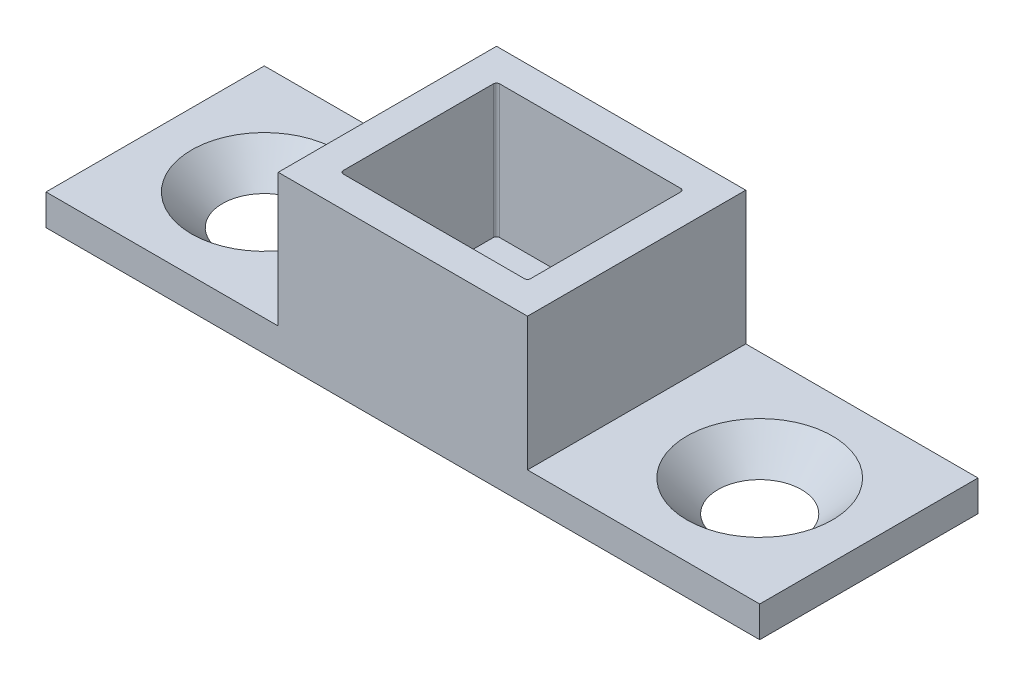
SolidWorks part; units mm, degrees
ref_plane "Front Plane" through (0, 0, 0) normal (0, 0, 1) x (1, 0, 0)
ref_plane "Top Plane" through (0, 0, 0) normal (0, 1, 0) x (1, 0, 0)
ref_plane "Right Plane" through (0, 0, 0) normal (1, 0, 0) x (0, 0, -1)
sketch "Sketch1" plane through (0, 0, 0) normal (0, 1, 0) x (1, 0, 0)
  line L0 (0, 5.05) -> (0, 7.05) construction
  line L1 (-8.05, 7.05) -> (8.05, 7.05)
  line L2 (-8.05, 7.05) -> (-8.05, -7.05)
  line L3 (-8.05, -7.05) -> (8.05, -7.05)
  line L4 (8.05, 7.05) -> (8.05, -7.05)
  line L5 (0, -5.05) -> (0, 0) construction
  line L6 (-8.05, 0) -> (-6.05, 0) construction
  line L11 (0, -5.05) -> (0, 0) construction
  line L12 (0, 0) -> (6.05, 0) construction
  line L13 (0, 0) -> (6.05, 0) construction
  point P233 (0, 0)
  point P296 (0, 0)
  dimension "D1" = 16.1
  dimension "D2" = 14.1
extrude "Boss-Extrude1" add sketch "Sketch1" along normal blind 10.6
sketch "Sketch3" plane through (0, 10.6, 0) normal (0, 1, 0) x (1, 0, 0)
  line L0 (-3.85, 0) -> (3.85, 0) construction
  line L1 (-6.05, 5.05) -> (6.05, 5.05)
  line L2 (-6.05, 5.05) -> (-6.05, -5.05)
  line L3 (-6.05, -5.05) -> (6.05, -5.05)
  line L4 (6.05, 5.05) -> (6.05, -5.05)
  line L5 (0, -5.05) -> (0, 5.05) construction
  line L6 (-6.05, 0) -> (6.05, 0) construction
  line L7 (0, -3.85) -> (0, 3.85) construction
  point P316 (0, 0)
  dimension "D1" = 10.1
  dimension "D2" = 12.1
extrude "Cut-Extrude1" cut sketch "Sketch3" against normal offset from surface (8.6 mm away) 2 up to plane "Top Plane"
hole_wizard "CSK for M1.6 Countersunk Flat Head Screw1" positions "Sketch6" profile "Sketch7" countersink size "M1.6" standard "ISO" end condition up to next
sketch "Sketch6" plane through (0, 0, 0) normal (0, -1, 0) x (-1, 0, 0)
  line L0 (-3.85, 0) -> (3.85, 0) construction
  line L1 (0, 3.85) -> (0, -3.85) construction
  point P0 (4.5, 0)
  point P9 (-4.5, 0)
  dimension "D1" = 4.5
sketch "Sketch7" plane through (-4.5, 0, 0) normal (1, 0, 0) x (0, 0, -1)
  line L0 (0, 0) -> (0, 2)
  line L1 (0, 2) -> (1, 2)
  line L2 (1, 2) -> (1, 1)
  line L3 (1, 1) -> (2, 0)
  line L5 (2, 0) -> (0, 0)
  line L6 (-1, 1) -> (-2, 0) construction
  line L11 (0, -6.35) -> (0, 107.95) construction
  dimension "Thru Hole Dia." = 2
  dimension "Thru Hole Depth" = 2
  dimension "Near C'Sink Dia." = 4
  dimension "Near C'Sink Angle" = 90
sketch "Sketch8" plane through (0, 2, 0) normal (0, 1, 0) x (1, 0, 0)
  circle A0 centre (0, 0) radius 2.25
  dimension "D1" = 4.5
extrude "Cut-Extrude2" cut sketch "Sketch8" against normal through all
fillet "Fillet2" radius 0.2 4 edges at (-6.05, 6.3, -5.05) (6.05, 6.3, -5.05) (-6.05, 6.3, 5.05) (6.05, 6.3, 5.05)
sketch "Sketch9" plane through (0, 0, 0) normal (0, 1, 0) x (1, 0, 0)
  line L0 (-8.05, 7.05) -> (-8.05, -7.05) construction
  line L1 (-8.05, 7.05) -> (-23.05, 7.05)
  line L2 (-8.05, 7.05) -> (-8.05, -7.05)
  line L3 (-8.05, -7.05) -> (-23.05, -7.05)
  line L4 (-23.05, 7.05) -> (-23.05, -7.05)
  line L5 (-15.55, -7.05) -> (-15.55, 7.05) construction
  line L6 (-8.05, 0) -> (-23.05, 0) construction
  line L7 (8.05, 7.05) -> (-8.05, 7.05) construction
  point P340 (-15.55, 0)
  dimension "D1" = 15
extrude "Boss-Extrude2" add sketch "Sketch9" along normal blind 2
hole_wizard "CSK for M4 Countersunk Flat Head Screw1" positions "Sketch10" profile "Sketch11" countersink size "M4" standard "ISO" end condition up to next
sketch "Sketch10" plane through (0, 2, 0) normal (0, 1, 0) x (1, 0, 0)
  line L0 (-5.83, 0) -> (5.83, 0) construction
  line L1 (0, -5.83) -> (0, 5.83) construction
  point P0 (-16, 0)
  dimension "D1" = 16
sketch "Sketch11" plane through (-16, 2, 0) normal (1, 0, 0) x (0, 0, 1)
  line L0 (0, 0) -> (0, 2.001)
  line L1 (0, 2.001) -> (2.4, 2.001)
  line L2 (2.4, 2.001) -> (2.4, 2.3)
  line L3 (2.4, 2.3) -> (4.7, 0)
  line L5 (4.7, 0) -> (0, 0)
  line L6 (-2.4, 2.3) -> (-4.7, 0) construction
  line L11 (0, -6.35) -> (0, 107.95) construction
  dimension "Thru Hole Dia." = 4.8
  dimension "Thru Hole Depth" = 2.001
  dimension "Near C'Sink Dia." = 9.4
  dimension "Near C'Sink Angle" = 90
mirror "Mirror1" about plane through (0, 0, 0) normal (1, 0, 0) of "Boss-Extrude2", "CSK for M4 Countersunk Flat Head Screw1"
